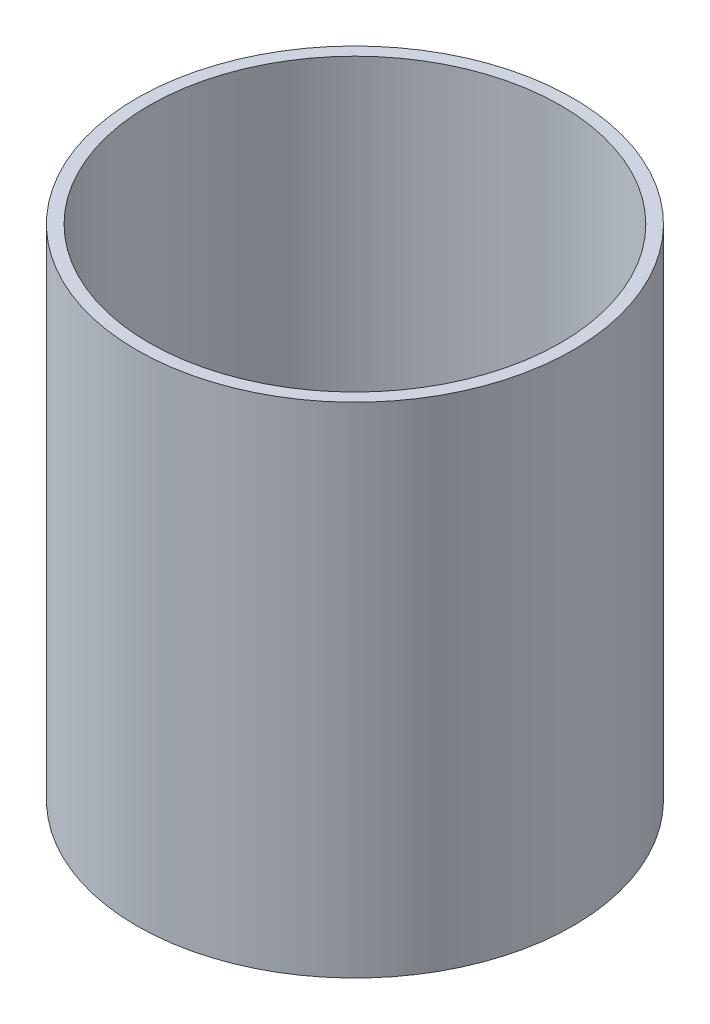
SolidWorks part; units mm, degrees
ref_plane "Front Plane" through (0, 0, 0) normal (0, 0, 1) x (1, 0, 0)
ref_plane "Top Plane" through (0, 0, 0) normal (0, 1, 0) x (1, 0, 0)
ref_plane "Right Plane" through (0, 0, 0) normal (1, 0, 0) x (0, 0, -1)
sketch "Sketch1" plane through (0, 0, 0) normal (0, 1, 0) x (1, 0, 0)
  circle A0 centre (0, 0) radius 22.225
  circle A1 centre (0, 0) radius 20.955
  dimension "D1" = 44.45
  dimension "D2" = 1.27
extrude "Boss-Extrude1" add sketch "Sketch1" along normal blind 50.8
